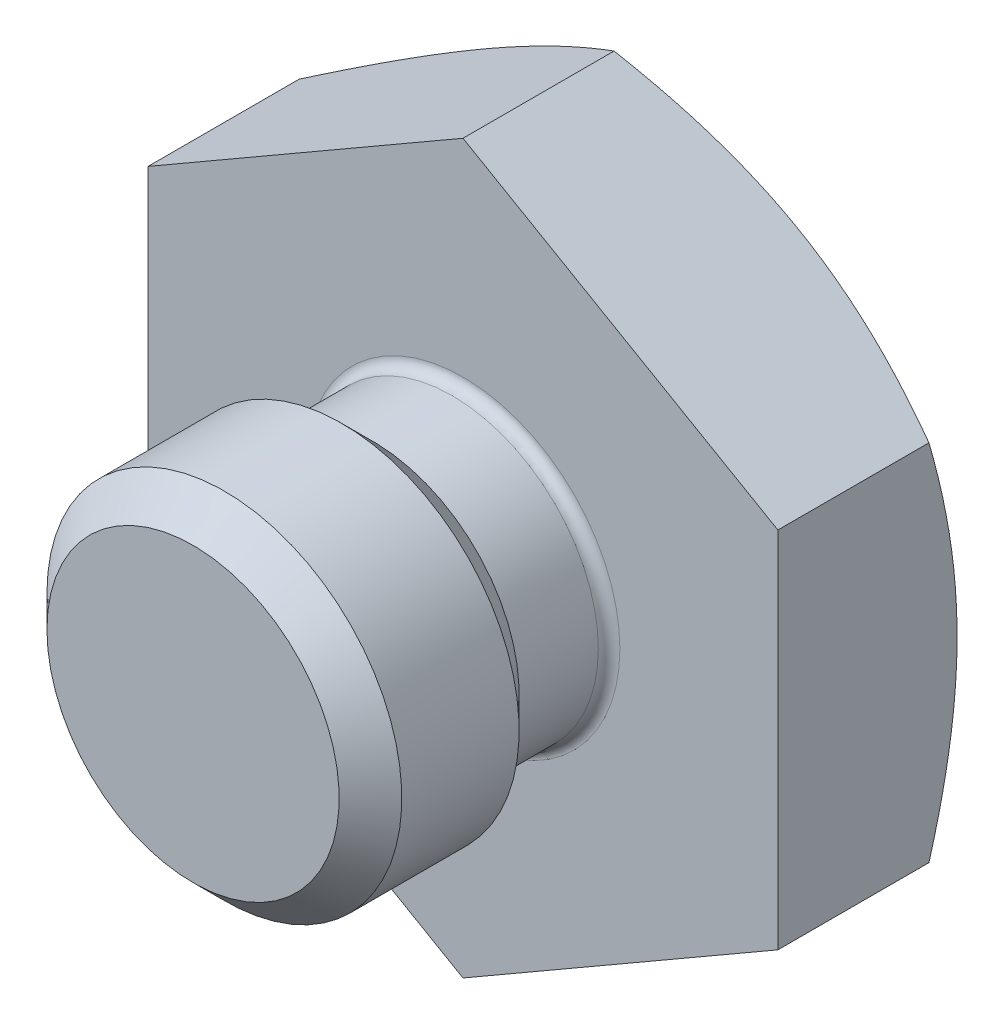
SolidWorks part; units mm, degrees
material "Alloy Steel"
ref_plane "Front Plane" through (0, 0, 0) normal (0, 0, 1) x (1, 0, 0)
ref_plane "Top Plane" through (0, 0, 0) normal (0, 1, 0) x (1, 0, 0)
ref_plane "Right Plane" through (0, 0, 0) normal (1, 0, 0) x (0, 0, -1)
sketch "Sketch1" plane through (0, 0, 0) normal (1, 0, 0) x (0, 0, -1)
  line L0 (0, 0) -> (-83.4165, 0) construction
  line L1 (0, 22.0651) -> (0, 5.1562)
  line L2 (0, 5.1562) -> (-3.175, 5.1562)
  line L3 (-3.175, 5.1562) -> (-4.2799, 6.2611)
  line L4 (-4.2799, 6.2611) -> (-8.4201, 6.2611)
  line L5 (-8.4201, 6.2611) -> (-9.525, 5.1562)
  line L6 (-9.525, 5.1562) -> (-9.525, 0)
  line L7 (-9.525, 0) -> (12.7, 0)
  line L8 (0, 22.0651) -> (12.666, 0.127)
  arc A0 (12.7, 0) -> (12.666, 0.127) centre (12.446, 0) ccw
  dimension "D1" = 12.7
  dimension "D7" = 0.254
  dimension "D2" = 12.5222
  dimension "D3" = 45
  dimension "D4" = 10.3124
  dimension "D5" = 3.175
  dimension "D6" = 60
  dimension "D8" = 9.525
revolve "Revolve1" add sketch "Sketch1" angle 360 about L0
sketch "Sketch2" plane through (0, 0, 0) normal (0, 0, 1) x (1, 0, 0)
  line L1 (0, 12.8316) -> (-11.1125, 6.4158)
  line L2 (-11.1125, 6.4158) -> (-11.1125, -6.4158)
  line L3 (-11.1125, -6.4158) -> (0, -12.8316)
  line L4 (0, -12.8316) -> (11.1125, -6.4158)
  line L5 (11.1125, -6.4158) -> (11.1125, 6.4158)
  line L6 (11.1125, 6.4158) -> (0, 12.8316)
  circle A0 centre (0, 0) radius 11.1125 construction
  dimension "D1" = 22.225
extrude "Cut-Extrude1" cut sketch "Sketch2" against normal through all flip side to cut
fillet "Fillet1" radius 0.381 1 edges at (-5.1562, 0, 0)
